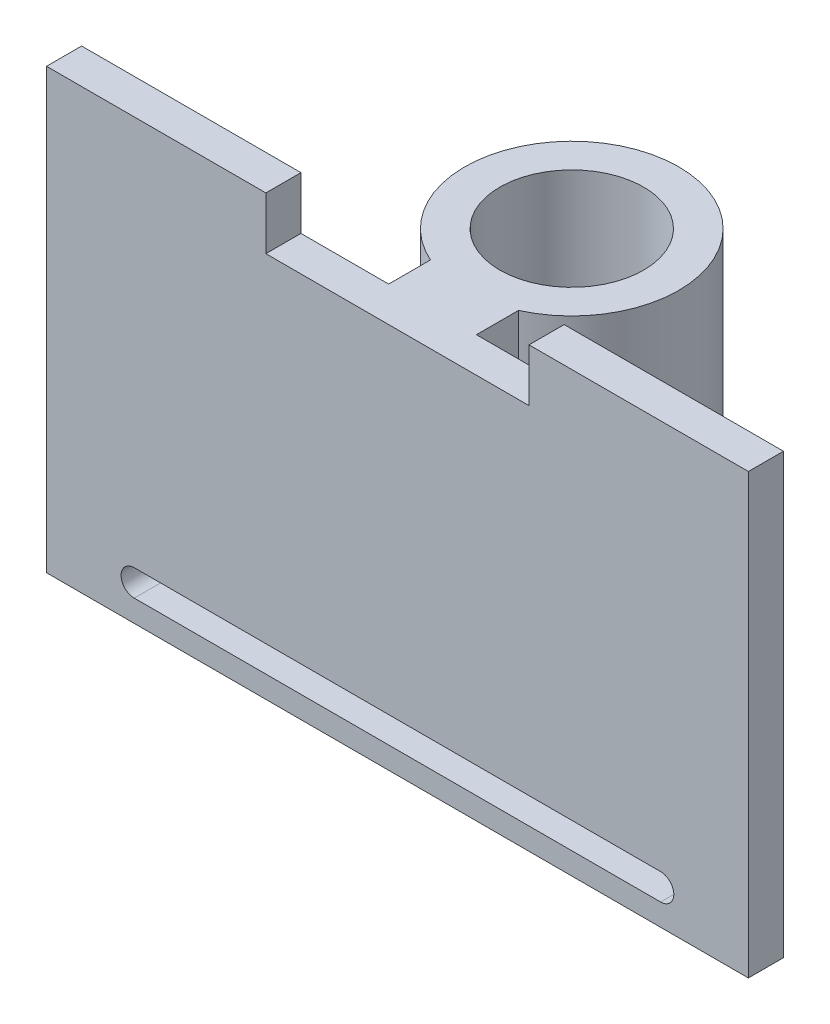
SolidWorks part; units mm, degrees
ref_plane "前视基准面" through (0, 0, 0) normal (0, 0, 1) x (1, 0, 0)
ref_plane "上视基准面" through (0, 0, 0) normal (0, 1, 0) x (1, 0, 0)
ref_plane "右视基准面" through (0, 0, 0) normal (1, 0, 0) x (0, 0, -1)
other "Configuration Table"
sketch "草图1" plane through (0, 0, 0) normal (0, 0, 1) x (1, 0, 0)
  line L0 (27.3314, -0.7115) -> (-12.6686, -0.7115) construction
  line L1 (-12.6686, 22.2885) -> (-0.1686, 22.2885)
  line L2 (-12.6686, 22.2885) -> (-12.6686, -2.7115)
  line L3 (-12.6686, -2.7115) -> (27.3314, -2.7115)
  line L4 (27.3314, 22.2885) -> (27.3314, -2.7115)
  line L5 (-12.6686, 9.7885) -> (27.3314, 9.7885) construction
  line L6 (-7.6686, -0.7115) -> (22.3314, -0.7115) construction
  line L7 (14.8314, 22.2885) -> (27.3314, 22.2885)
  line L8 (-7.6686, 0.0385) -> (22.3314, 0.0385)
  line L9 (-7.6686, -1.4615) -> (22.3314, -1.4615)
  line L11 (-0.1686, 22.2885) -> (-0.1686, 19.2885)
  line L12 (-0.1686, 19.2885) -> (14.8314, 19.2885)
  line L13 (14.8314, 22.2885) -> (14.8314, 19.2885)
  arc A0 (-7.6686, 0.0385) -> (-7.6686, -1.4615) centre (-7.6686, -0.7115) ccw
  arc A1 (22.3314, -1.4615) -> (22.3314, 0.0385) centre (22.3314, -0.7115) ccw
  point P12 (7.3314, -0.7115)
  dimension "D1" = 25
  dimension "D2" = 40
  dimension "D3" = 2
  dimension "D4" = 30
  dimension "D5" = 15
  dimension "D6" = 3
extrude "凸台-拉伸1" add sketch "草图1" along normal blind 2
sketch "草图2" plane through (0, 19.2885, 0) normal (0, 1, 0) x (1, 0, 0)
  line L0 (14.8314, 0) -> (-0.1686, 0) construction
  line L2 (4.8314, 2.3811) -> (4.8314, 0)
  line L3 (4.8314, 0) -> (9.8314, 0)
  line L4 (9.8314, 2.3993) -> (9.8314, 0)
  circle A0 centre (7.3111, 7.9543) radius 4.1
  arc A1 (9.8314, 2.3993) -> (4.8314, 2.3811) centre (7.3111, 7.9543) ccw
  circle A2 centre (7.3111, 7.9543) radius 6.1 construction
  point P6 (7.3314, 0)
  point P7 (7.3314, 0)
  point P10 (0, 0)
  point P11 (0, 0)
  dimension "D1" = 8.2
  dimension "D4" = 2
extrude "凸台-拉伸2" add sketch "草图2" against normal blind 15 contours L2 L3 L4 A1 | A0
